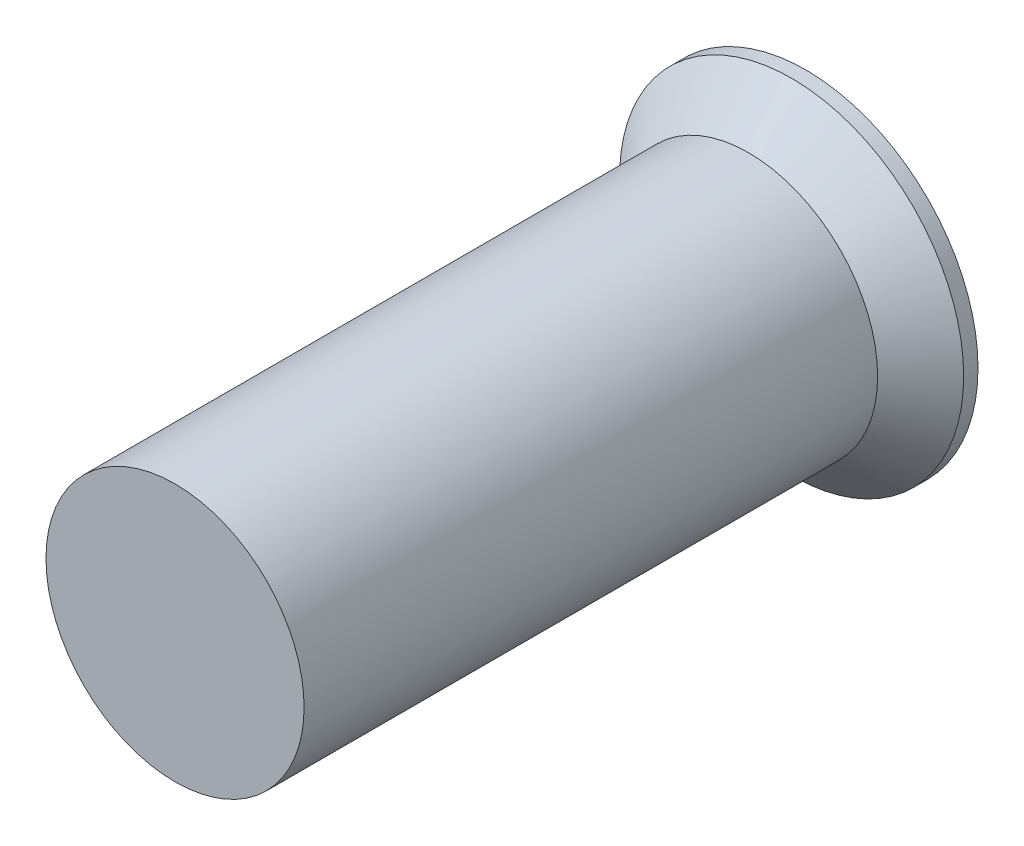
SolidWorks part; units mm, degrees
ref_plane "Plan de face" through (0, 0, 0) normal (0, 0, 1) x (1, 0, 0)
ref_plane "Plan de dessus" through (0, 0, 0) normal (0, 1, 0) x (1, 0, 0)
ref_plane "Plan de droite" through (0, 0, 0) normal (1, 0, 0) x (0, 0, -1)
sketch "Esquisse1" plane through (0, 0, 0) normal (0, 0, 1) x (1, 0, 0)
  circle A0 centre (0, 0) radius 3
  dimension "D1" = 6
extrude "Boss.-Extru.1" add sketch "Esquisse1" along normal blind 1
chamfer "Chanfrein1" distance 0.75 angle 45 1 edges at (3, 0, 1)
sketch "Esquisse2" plane through (0, 0, 1) normal (0, 0, 1) x (1, 0, 0)
  circle A1 centre (0, 0) radius 2.25
  dimension "D1" = 4.5
extrude "Boss.-Extru.2" add sketch "Esquisse2" along normal blind 10
